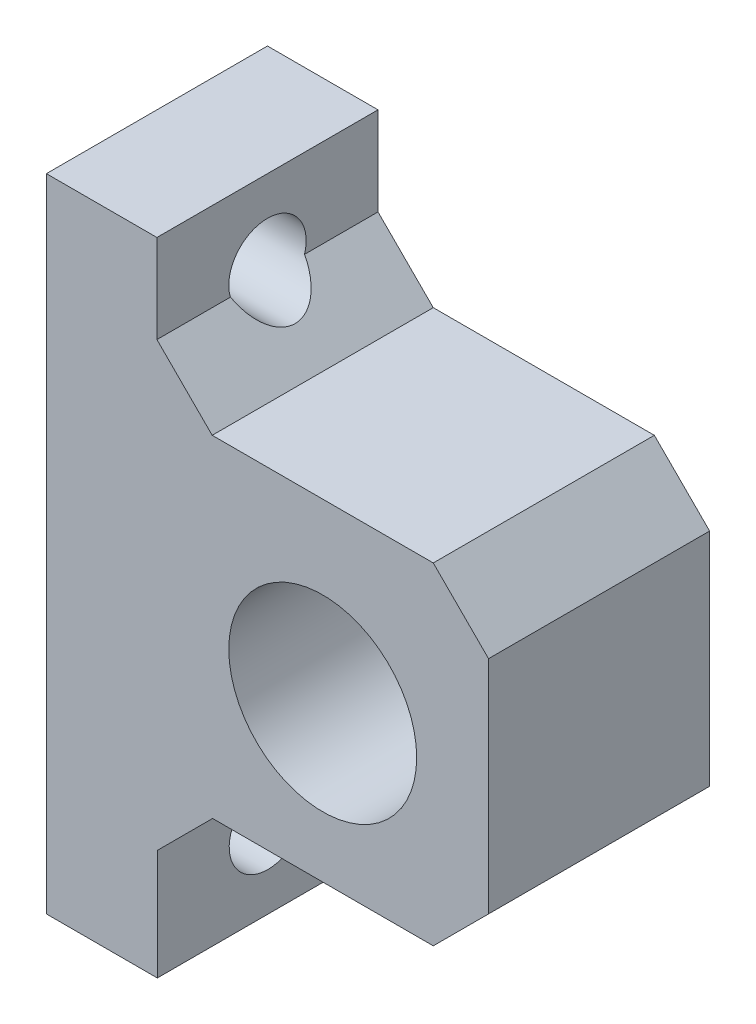
SolidWorks part; units mm, degrees
ref_plane "Front Plane" through (0, 0, 0) normal (0, 0, 1) x (1, 0, 0)
ref_plane "Top Plane" through (0, 0, 0) normal (0, 1, 0) x (1, 0, 0)
ref_plane "Right Plane" through (0, 0, 0) normal (1, 0, 0) x (0, 0, -1)
sketch "Sketch1" plane through (0, 0, 0) normal (0, 0, 1) x (1, 0, 0)
  line L0 (3.6965, -34.4358) -> (3.6965, -19.4358)
  line L1 (-6.3408, 23.5642) -> (3.6592, 23.5642)
  line L2 (-6.3408, 23.5642) -> (-6.3408, -34.4358)
  line L3 (-6.3408, -34.4358) -> (3.6965, -34.4358)
  line L4 (3.6592, 23.5642) -> (3.6592, 10.5642)
  line L5 (3.6592, 10.5642) -> (33.6592, 10.5642)
  line L7 (3.6965, -19.4358) -> (33.6592, -19.4358)
  line L8 (33.6592, 10.5642) -> (33.6592, -19.4358)
  circle A0 centre (18.6592, -5.4358) radius 8.5
  dimension "D8" = 17
  dimension "D1" = 58
  dimension "D2" = 10
  dimension "D3" = 29
  dimension "D4" = 30
  dimension "D5" = 15
  dimension "D6" = 40
  dimension "D7" = 15
extrude "Boss-Extrude1" add sketch "Sketch1" along normal blind 20
chamfer "Chamfer1" distance 5 angle 45 4 edges at (3.6965, -19.4358, 10) (33.6592, -19.4358, 10) (33.6592, 10.5642, 10) (3.6592, 10.5642, 10)
sketch "Sketch2" plane through (-6.3408, 0, 0) normal (-1, 0, 0) x (0, 0, 1)
  line L0 (20, 23.5642) -> (0, 23.5642) construction
  line L1 (20, 23.5642) -> (20, -34.4358) construction
  circle A0 centre (10, 16.5642) radius 3.5
  dimension "D3" = 7
  dimension "D1" = 7
  dimension "D2" = 10
extrude "Cut-Extrude1" cut sketch "Sketch2" against normal blind 20
pattern_linear "LPattern1" count 200 spacing 44 along (0, -1, 0) of "Cut-Extrude1"
